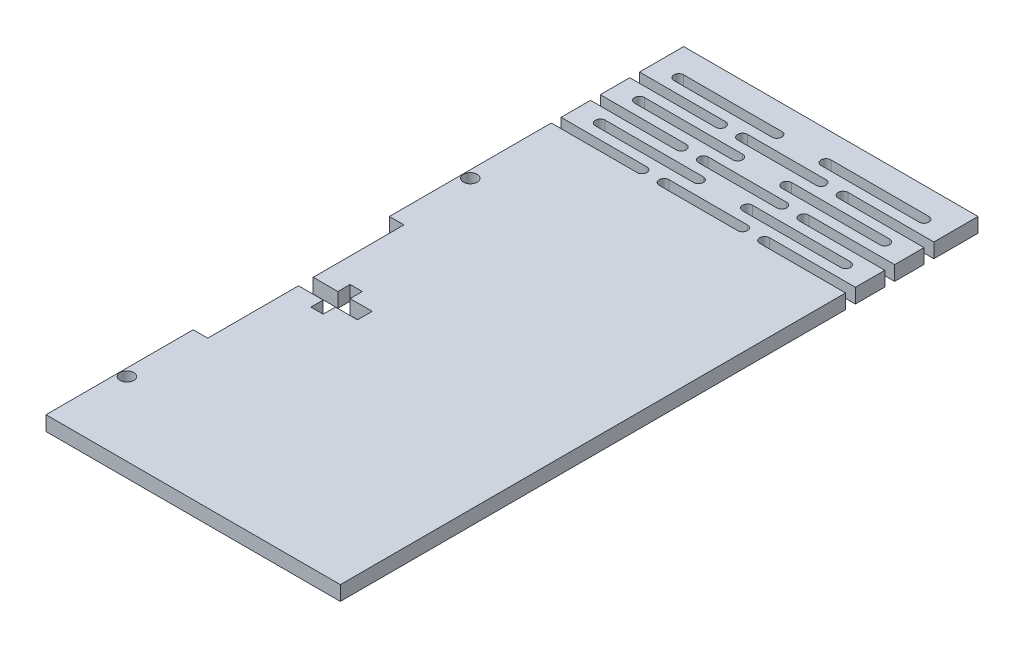
SolidWorks part; units mm, degrees
ref_plane "Front" through (0, 0, 0) normal (0, 0, 1) x (1, 0, 0)
ref_plane "Top" through (0, 0, 0) normal (0, 1, 0) x (1, 0, 0)
ref_plane "Right" through (0, 0, 0) normal (1, 0, 0) x (0, 0, -1)
sketch "草图1" plane through (0, 0, 0) normal (0, 1, 0) x (1, 0, 0)
  line L1 (30, -50) -> (-30, -50)
  line L2 (30, -50) -> (30, 50)
  line L3 (30, 50) -> (-30, 50)
  line L4 (-30, -50) -> (-30, 50)
  line L5 (30, -50) -> (-30, 50) construction
  line L6 (30, 50) -> (-30, -50) construction
  line L7 (-27.0282, 40) -> (-30, 40)
  line L8 (-77.0282, 100) -> (-80, 100)
  line L9 (-77.0282, 90) -> (-80, 90)
  line L10 (-77.0282, 80) -> (-80, 80)
  line L11 (-77.0282, 70) -> (-80, 70)
  line L12 (-77.0282, 60) -> (-80, 60)
  line L13 (-77.0282, 50) -> (-80, 50)
  line L14 (-77.0282, 40) -> (-80, 40)
  line L15 (-77.0282, 30) -> (-80, 30)
  line L16 (-77.0282, 20) -> (-80, 20)
  line L17 (-77.0282, 10) -> (-80, 10)
  line L18 (-77.0282, 0) -> (-80, 0)
  line L19 (-77.0282, -10) -> (-80, -10)
  line L20 (-77.0282, -20) -> (-80, -20)
  line L21 (-77.0282, -30) -> (-80, -30)
  line L22 (-77.0282, -40) -> (-80, -40)
  line L23 (-77.0282, -50) -> (-80, -50)
  line L24 (-77.0282, -60) -> (-80, -60)
  line L25 (-77.0282, -70) -> (-80, -70)
  line L26 (-77.0282, -80) -> (-80, -80)
  line L27 (-77.0282, -90) -> (-80, -90)
  line L28 (-77.0282, -100) -> (-80, -100)
  line L29 (-77.0282, -110) -> (-80, -110)
  line L30 (-27.0282, -50) -> (-30, -50)
  line L31 (0, 0) -> (0, 50)
  line L32 (0, 0) -> (0, -50)
  point P0 (0, 0)
  dimension "D1" = 60
  dimension "D2" = 100
  dimension "D4" = 10
extrude "凸台-拉伸1" add sketch "草图1" along normal blind 2.9718
sketch "草图2" plane through (0, 0, 0) normal (0, -1, 0) x (-1, 0, 0)
  line L0 (30, -50) -> (30, 50) construction
  line L1 (27.0282, 20) -> (30, 20)
  line L2 (27.0282, 20) -> (27.0282, -20)
  line L3 (27.0282, -20) -> (30, -20)
  line L4 (30, 20) -> (30, -20)
  line L5 (-30, -50) -> (30, -50) construction
  dimension "D1" = 40
  dimension "D2" = 30
  dimension "D3" = 2.9718
extrude "切除-拉伸1" cut sketch "草图2" against normal blind 10
sketch "草图3" plane through (0, 0, 0) normal (0, -1, 0) x (-1, 0, 0)
  line L0 (-30, -50) -> (-30, 50) construction
  line L1 (-30, 50) -> (30, 50)
  line L2 (-30, 50) -> (-30, 80)
  line L3 (-30, 80) -> (30, 80)
  line L4 (30, 50) -> (30, 80)
  line L5 (-12.5, 55.0025) -> (-30, 55.0025)
  line L6 (-30, 53.0025) -> (-12, 53.0025)
  line L7 (-9, 50) -> (51, 50)
  line L8 (-8, 55.0025) -> (8, 55.0025)
  line L9 (-8, 53.0025) -> (8, 53.0025)
  line L10 (12, 50) -> (72, 50)
  line L11 (12, 53.0025) -> (30, 53.0025)
  line L12 (29.5, 55.0025) -> (12, 55.0025)
  line L13 (29.5, 55.0025) -> (30, 55.0025)
  circle A0 centre (-30, 54.0025) radius 1
  circle A1 centre (-12.5, 54.0025) radius 1
  circle A2 centre (8, 54.0025) radius 1
  circle A3 centre (-8, 54.0025) radius 1
  circle A4 centre (30, 54.0025) radius 1
  circle A5 centre (12.5, 54.0025) radius 1
  dimension "D3" = 2
  dimension "D4" = 2
  dimension "D8" = 4.5
  dimension "D1" = 60
  dimension "D2" = 30
  dimension "D5" = 0
  dimension "D6" = 17.5
  dimension "D7" = 17.5
  dimension "D9" = 16
sketch "草图4" plane through (0, 0, 0) normal (0, -1, 0) x (1, 0, 0)
  line L1 (30, -50) -> (-30, -50)
  line L2 (30, -50) -> (30, -80)
  line L3 (30, -80) -> (-30, -80)
  line L4 (-30, -50) -> (-30, -80)
extrude "凸台-拉伸2" add sketch "草图4" against normal blind 2.9718
extrude "切除-拉伸2" cut sketch "草图3" against normal blind 2.9718
pattern_linear "阵列(线性)1" count 3 spacing 8 along (0, 0, -1) of "切除-拉伸2"
sketch "草图5" plane through (0, 0, 0) normal (0, -1, 0) x (1, 0, 0)
  line L0 (-12.5, -55.0025) -> (-30, -55.0025) construction
  line L1 (12.5, -55.0025) -> (30, -55.0025) construction
  line L2 (-30, -55.0025) -> (-30, -61.0025) construction
  line L3 (-30, -80) -> (30, -80) construction
  line L4 (-25, -57.0025) -> (-5, -57.0025)
  line L5 (-25, -59.0025) -> (-5, -59.0025)
  circle A1 centre (-5, -58.0025) radius 1
  circle A2 centre (-25, -58.0025) radius 1
  point P12 (0, -80)
  dimension "D1" = 2
  dimension "D2" = 2
  dimension "D3" = 3
  dimension "D4" = 3
  dimension "D5" = 5
  dimension "D6" = 5
extrude "切除-拉伸3" cut sketch "草图5" against normal blind 10 contours A2 L5 A1 L4 | A2 | A1
pattern_linear "阵列(线性)2" count 3 spacing 8 along (0, 0, -1) count 2 spacing 30 along (1, 0, 0) of "切除-拉伸3"
sketch "草图7" plane through (0, 0, 0) normal (0, -1, 0) x (1, 0, 0)
  line L0 (-30, -1.5) -> (-22, -1.5)
  line L1 (-30, 50) -> (-30, 20) construction
  line L2 (-22, -1.5) -> (-22, -4)
  line L3 (-22, -4) -> (-19.5, -4)
  line L4 (-19.5, -4) -> (-19.5, -1.5)
  line L5 (-19.5, -1.5) -> (-15, -1.5)
  line L6 (-15, -1.5) -> (-15, 1.5)
  line L13 (-15, 0) -> (-30, 0)
  line L14 (30, 50) -> (-30, 50) construction
  line L15 (-30, 1.5) -> (-30, -1.5)
  line L16 (-19.5, 1.5) -> (-15, 1.5)
  line L17 (-22, 4) -> (-19.5, 4)
  line L18 (-19.5, 4) -> (-19.5, 1.5)
  line L19 (-30, 1.5) -> (-22, 1.5)
  line L20 (-22, 1.5) -> (-22, 4)
  point P17 (-22.5, 0)
  dimension "D1" = 50
  dimension "D2" = 15
  dimension "D3" = 1.5
  dimension "D4" = 1.5
  dimension "D5" = 2.5
  dimension "D6" = 8
  dimension "D7" = 4
extrude "切除-拉伸4" cut sketch "草图7" against normal blind 10 contours L20 L19 L15 L13 L6 L16 L18 L17 | L13 L15 L0 L2 L3 L4 L5 L6
sketch "草图8" plane through (0, 0, 0) normal (0, -1, 0) x (-1, 0, 0)
  line L0 (30, -50) -> (30, -20) construction
  line L1 (-30, -50) -> (30, -50) construction
  circle A0 centre (28.5, -35) radius 1.4
  dimension "D1" = 2.8
  dimension "D2" = 1.5
  dimension "D3" = 15
extrude "切除-拉伸5" cut sketch "草图8" against normal blind 10
pattern_linear "阵列(线性)3" count 4 spacing 70 along (0, 0, -1) of "切除-拉伸5"
